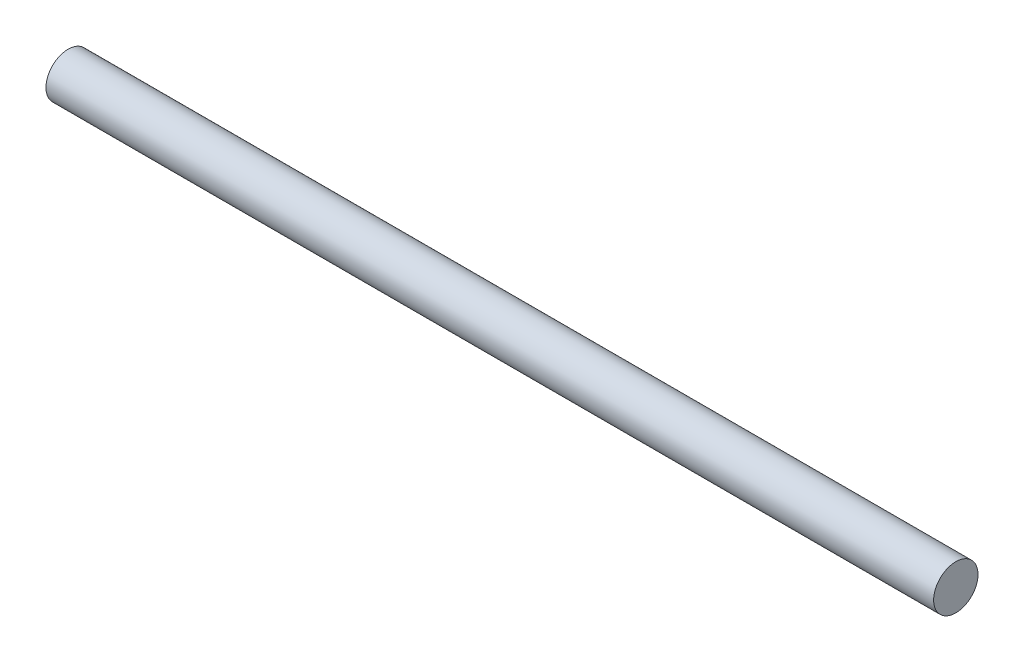
SolidWorks part; units mm, degrees
ref_plane "Front Plane" through (0, 0, 0) normal (0, 0, 1) x (1, 0, 0)
ref_plane "Top Plane" through (0, 0, 0) normal (0, 1, 0) x (1, 0, 0)
ref_plane "Right Plane" through (0, 0, 0) normal (1, 0, 0) x (0, 0, -1)
sketch "Sketch1" plane through (0, 0, 0) normal (1, 0, 0) x (0, 0, -1)
  circle A0 centre (0, 0) radius 1
  dimension "D1" = 2
extrude "Boss-Extrude1" add sketch "Sketch1" along normal mid plane 40
